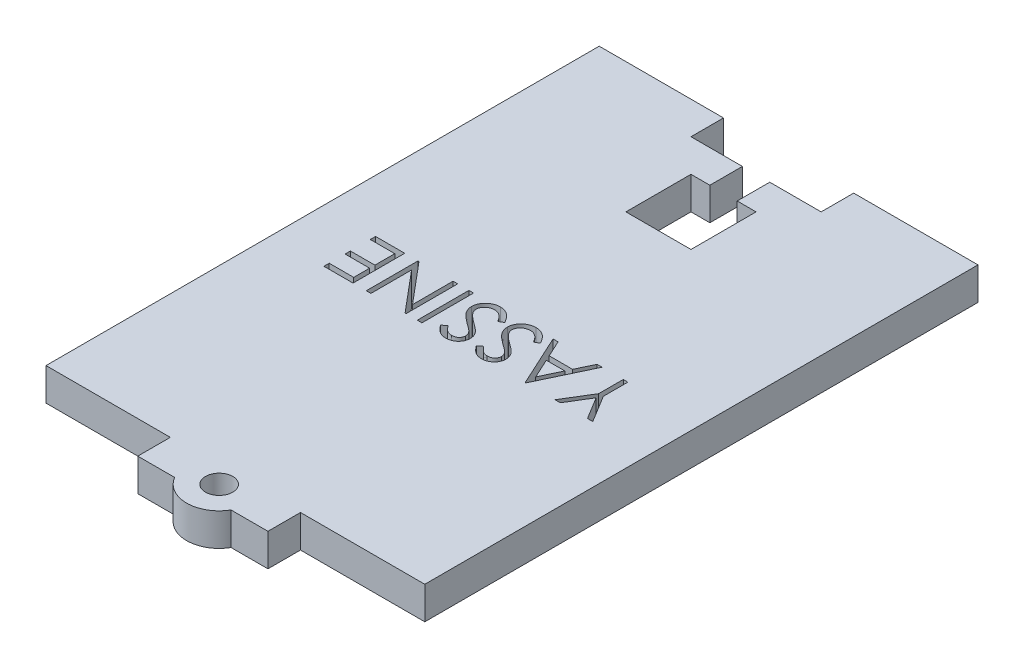
SolidWorks part; units mm, degrees
ref_plane "Front Plane" through (0, 0, 0) normal (0, 0, 1) x (1, 0, 0)
ref_plane "Top Plane" through (0, 0, 0) normal (0, 1, 0) x (1, 0, 0)
ref_plane "Right Plane" through (0, 0, 0) normal (1, 0, 0) x (0, 0, -1)
sketch "Sketch1" plane through (0, 0, 0) normal (0, 0, 1) x (1, 0, 0)
  line L0 (93.3354, 78.0569) -> (93.3354, 64.5889) construction
  line L1 (122.4354, 70.5569) -> (103.3354, 70.5569)
  line L2 (122.4354, 70.5569) -> (122.4354, 75.5569)
  line L3 (122.4354, 75.5569) -> (103.3354, 75.5569)
  line L6 (64.2354, 75.5569) -> (83.3354, 75.5569)
  line L7 (64.2354, 70.5569) -> (64.2354, 75.5569)
  line L8 (64.2354, 70.5569) -> (83.3354, 70.5569)
  line L9 (103.3354, 70.5569) -> (83.3354, 70.5569)
  line L10 (83.3354, 75.5569) -> (103.3354, 75.5569)
  arc A0 (97.6655, 75.5569) -> (89.0052, 75.5569) centre (93.3354, 73.0569) ccw construction
extrude "Boss-Extrude1" add sketch "Sketch1" along normal blind 80
sketch "Sketch2" plane through (0, 0, 0) normal (0, 0, -1) x (-1, 0, 0)
  line L0 (-64.2354, 70.5569) -> (-122.4354, 70.5569) construction
  line L1 (-122.4354, 75.5569) -> (-103.3354, 75.5569)
  line L2 (-122.4354, 75.5569) -> (-122.4354, 70.5569)
  line L3 (-122.4354, 70.5569) -> (-103.3354, 70.5569)
  line L4 (-103.3354, 75.5569) -> (-103.3354, 70.5569)
  line L5 (-103.3354, 75.5569) -> (-103.3354, 70.5569) construction
  line L6 (-83.3354, 75.5569) -> (-83.3354, 70.5569) construction
  line L7 (-64.2354, 75.5569) -> (-83.3354, 75.5569)
  line L8 (-64.2354, 75.5569) -> (-64.2354, 70.5569)
  line L9 (-64.2354, 70.5569) -> (-83.3354, 70.5569)
  line L10 (-83.3354, 75.5569) -> (-83.3354, 70.5569)
extrude "Boss-Extrude2" add sketch "Sketch2" along normal blind 5
sketch "Sketch3" plane through (0, 0, 80) normal (0, 0, 1) x (1, 0, 0)
  line L1 (83.3354, 70.5569) -> (103.3354, 70.5569)
  line L2 (83.3354, 70.5569) -> (83.3354, 75.5569)
  line L3 (83.3354, 75.5569) -> (103.3354, 75.5569)
  line L4 (103.3354, 70.5569) -> (103.3354, 75.5569)
extrude "Boss-Extrude3" add sketch "Sketch3" along normal blind 5
sketch "Sketch4" plane through (0, 75.5569, 0) normal (0, 1, 0) x (1, 0, 0)
  line L0 (83.3354, -85) -> (103.3354, -80) construction
  line L1 (103.3354, -85) -> (83.3354, -85) construction
  line L2 (97.6655, -85) -> (89.0052, -85)
  arc A0 (89.0052, -85) -> (97.6655, -85) centre (93.3354, -82.5) ccw
  dimension "D1" = 10
extrude "Boss-Extrude4" add sketch "Sketch4" against normal blind 5
sketch "Sketch5" plane through (0, 75.5569, 0) normal (0, 1, 0) x (1, 0, 0)
  line L0 (93.3354, 0) -> (93.3354, -5.3328) construction
  line L1 (103.3354, 0) -> (83.3354, 0) construction
  line L2 (91.2354, 0) -> (91.2354, -5)
  line L3 (91.2354, -5) -> (88.3354, -5)
  line L4 (88.3354, -5) -> (88.3354, -15)
  line L5 (88.3354, -15) -> (98.3354, -15)
  line L6 (98.3354, -15) -> (98.3354, -5)
  line L7 (98.3354, -5) -> (95.4354, -5)
  line L8 (95.4354, -5) -> (95.4354, 0)
  line L9 (91.2354, 0) -> (95.4354, 0)
  circle A0 centre (93.3354, -82.5) radius 2.1
  dimension "D1" = 4.2
  dimension "D2" = 2.1
  dimension "D3" = 4.2
  dimension "D4" = 5
  dimension "D5" = 10
  dimension "D6" = 10
  dimension "D7" = 5
extrude "Cut-Extrude1" cut sketch "Sketch5" against normal blind 5
sketch "Sketch6" plane through (0, 75.5569, 0) normal (0, 1, 0) x (1, 0, 0)
  line L0 (64.2354, -37.5) -> (122.4354, -37.5) construction
  line L1 (64.2354, -80) -> (64.2354, 5) construction
  line L2 (122.4354, -80) -> (122.4354, 5) construction
  text T0 "YASSINE" font "Century Gothic" height in points 30
extrude "Cut-Extrude2" cut sketch "Sketch6" against normal blind 5
